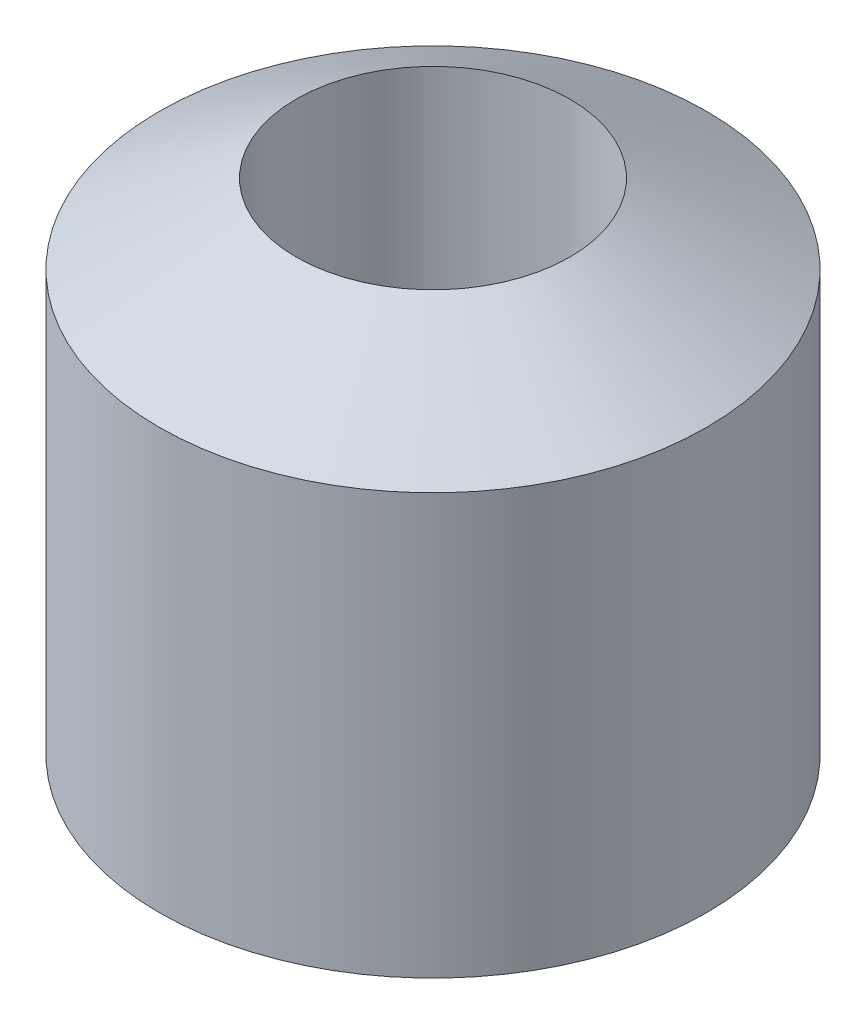
SolidWorks part; units mm, degrees
ref_plane "Front Plane" through (0, 0, 0) normal (0, 0, 1) x (1, 0, 0)
ref_plane "Top Plane" through (0, 0, 0) normal (0, 1, 0) x (1, 0, 0)
ref_plane "Right Plane" through (0, 0, 0) normal (1, 0, 0) x (0, 0, -1)
sketch "Sketch1" plane through (0, 0, 0) normal (1, 0, 0) x (0, 0, -1)
  line L0 (-33.7377, 0) -> (30.0656, 0) construction
  line L1 (0, 32.3607) -> (0, -46.7432) construction
  line L2 (14, 29.5829) -> (14, -29.5829)
  line L3 (14, 29.5829) -> (28, 21.5)
  line L4 (28, 21.5) -> (28, -21.5)
  line L6 (14, -29.5829) -> (28, -21.5)
  dimension "D1" = 14
  dimension "D2" = 28
  dimension "D3" = 60
  dimension "D4" = 43
revolve "Revolve1" add sketch "Sketch1" angle 360 about L1
